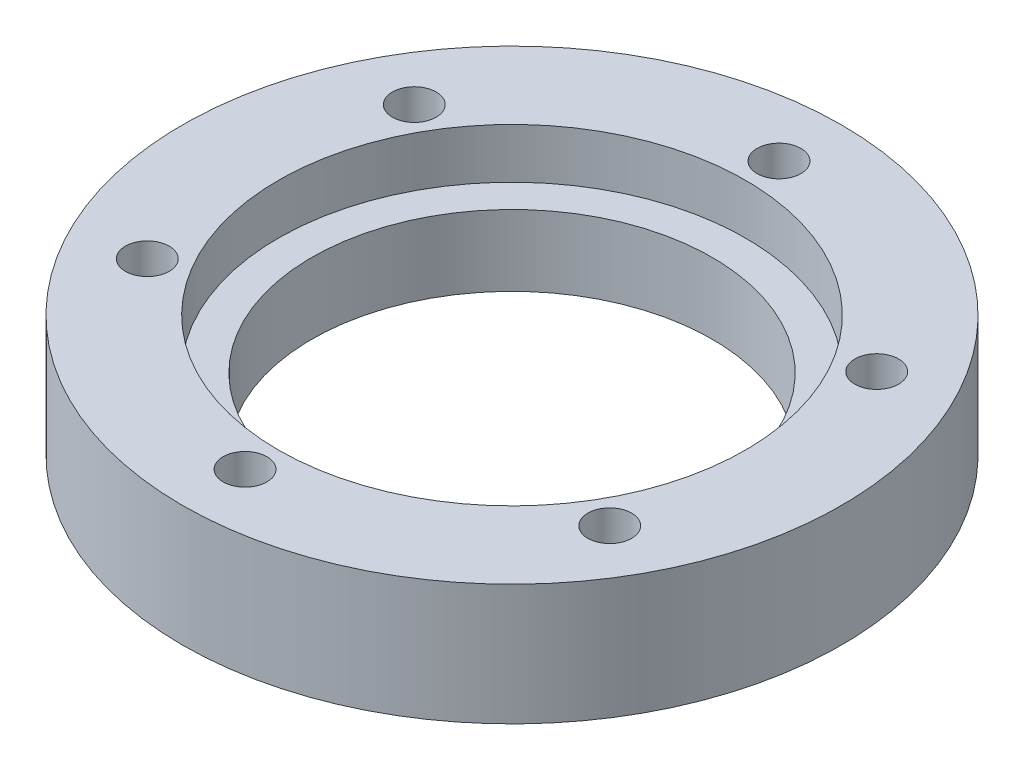
SolidWorks part; units mm, degrees
ref_plane "Front Plane" through (0, 0, 0) normal (0, 0, 1) x (1, 0, 0)
ref_plane "Top Plane" through (0, 0, 0) normal (0, 1, 0) x (1, 0, 0)
ref_plane "Right Plane" through (0, 0, 0) normal (1, 0, 0) x (0, 0, -1)
sketch "Sketch1" plane through (0, 0, 0) normal (0, 1, 0) x (1, 0, 0)
  circle A0 centre (0, 0) radius 79
extrude "Boss-Extrude1" add sketch "Sketch1" along normal blind 29
hole_wizard "CBORE for M10 Hex Head Bolt1" positions "Sketch2" profile "Sketch3" counterbore size "M10" standard "ANSI Metric" end condition through all
sketch "Sketch2" plane through (0, 29, 0) normal (0, 1, 0) x (1, 0, 0)
  point P0 (0, 0)
sketch "Sketch3" plane through (0, 29, 0) normal (1, 0, 0) x (0, 0, 1)
  line L0 (0, 0) -> (0, 29)
  line L1 (0, 29) -> (48, 29)
  line L3 (48, 29) -> (48, 12)
  line L4 (48, 12) -> (56, 12)
  line L5 (56, 12) -> (56, 0)
  line L7 (56, 0) -> (0, 0)
  line L11 (0, -6.35) -> (0, 107.95) construction
  dimension "Thru Hole Dia." = 96
  dimension "Thru Hole Depth" = 29
  dimension "C'Bore Dia." = 112
  dimension "C'Bore Depth" = 12
hole_wizard "Tap Drill for M12x1.5 Tap1" positions "Sketch4" profile "Sketch5" hole size "M12x1.5" standard "ANSI Metric" end condition through all
sketch "Sketch4" plane through (0, 29, 0) normal (0, 1, 0) x (1, 0, 0)
  line L0 (0, 0) -> (55.4256, -32) construction
  circle A0 centre (0, 0) radius 64 construction
  point P0 (55.4256, -32)
  point P23 (0, -64)
  point P24 (-55.4256, -32)
  point P25 (-55.4256, 32)
  point P26 (0, 64)
  point P27 (55.4256, 32)
  point P28 (0, 0)
  dimension "D1" = 6
sketch "Sketch5" plane through (55.4256, 29, 32) normal (1, 0, 0) x (0, 0, 1)
  line L0 (0, 0) -> (0, 29)
  line L1 (0, 29) -> (5.25, 29)
  line L2 (5.25, 29) -> (5.25, 0)
  line L5 (5.25, 0) -> (0, 0)
  line L11 (0, -6.35) -> (0, 107.95) construction
  dimension "Thru Hole Dia." = 10.5
  dimension "Thru Hole Depth" = 29
